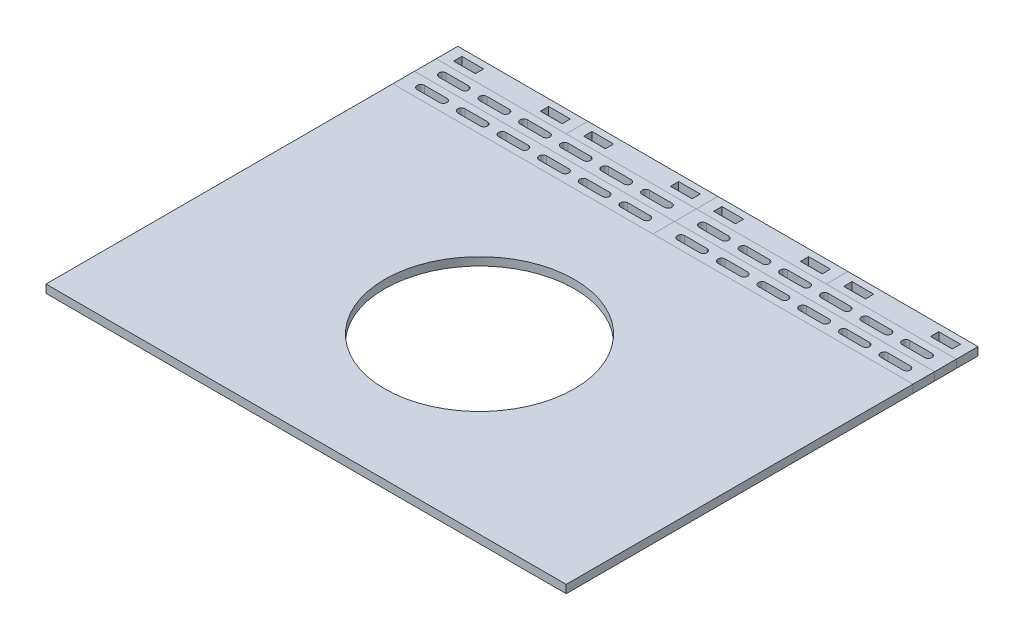
SolidWorks part; units mm, degrees
ref_plane "Front Plane" through (0, 0, 0) normal (0, 0, 1) x (1, 0, 0)
ref_plane "Top Plane" through (0, 0, 0) normal (0, 1, 0) x (1, 0, 0)
ref_plane "Right Plane" through (0, 0, 0) normal (1, 0, 0) x (0, 0, -1)
sketch "Sketch1" plane through (0, 0, 0) normal (0, 1, 0) x (1, 0, 0)
  line L0 (0, 0) -> (0, 203.2)
  line L1 (0, 0) -> (304.8, 0)
  line L5 (304.8, 203.2) -> (304.8, 0)
  line L6 (0, 203.2) -> (304.8, 203.2)
  line L7 (0, 101.6) -> (304.8, 101.6) construction
  line L8 (152.4, 203.2) -> (152.4, 0) construction
  circle A2 centre (152.4, 101.6) radius 55.5625
  point P11 (152.4, 101.6)
  dimension "D3" = 111.125
  dimension "D1" = 304.8
  dimension "D2" = 203.2
extrude "Boss-Extrude1" add sketch "Sketch1" along normal blind 4.7625
sketch "Sketch3" plane through (0, 0, 0) normal (0, 1, 0) x (1, 0, 0)
  line L0 (0, 203.2) -> (0, 215.9)
  line L1 (0, 215.9) -> (152.4, 215.9)
  line L2 (152.4, 215.9) -> (152.4, 203.2)
  line L3 (304.8, 203.2) -> (0, 203.2) construction
  line L4 (152.4, 203.2) -> (0, 203.2)
  dimension "D1" = 12.7
  dimension "D2" = 152.4
extrude "Boss-Extrude2" add sketch "Sketch3" along normal blind 4.7625 separate body
sketch "Sketch4" plane through (0, 4.7625, 0) normal (0, 1, 0) x (1, 0, 0)
  line L0 (10.0838, 209.55) -> (23.2537, 209.55) construction
  line L1 (10.0838, 211.6963) -> (23.2537, 211.6963)
  line L2 (10.0838, 207.4037) -> (23.2537, 207.4037)
  line L3 (10.0838, 215.9) -> (10.0838, 203.2) construction
  line L4 (152.4, 215.9) -> (0, 215.9) construction
  line L5 (304.8, 203.2) -> (0, 203.2) construction
  line L6 (7.9375, 209.55) -> (0, 209.55) construction
  line L7 (0, 215.9) -> (0, 203.2) construction
  arc A0 (10.0838, 211.6963) -> (10.0838, 207.4037) centre (10.0838, 209.55) ccw
  arc A1 (23.2537, 207.4037) -> (23.2537, 211.6963) centre (23.2537, 209.55) ccw
  point P2 (16.6687, 209.55)
  point P13 (25.4, 209.55)
  point P15 (10.0838, 209.55)
  dimension "D1" = 2.1463
  dimension "D2" = 7.9375
  dimension "D3" = 17.4625
extrude "Cut-Extrude1" cut sketch "Sketch4" against normal blind 4.7625
pattern_linear "LPattern2" count 6 spacing 23.8125 along (1, 0, 0) of "Cut-Extrude1"
pattern_linear "LPattern3" count 2 spacing 12.7 along (0, 0, -1) count 2 spacing 152.4 along (1, 0, 0) of bodies 104
sketch "Sketch5" plane through (0, 0, 0) normal (0, 1, 0) x (1, 0, 0)
  line L0 (0, 228.6) -> (0, 241.3)
  line L1 (0, 241.3) -> (76.2, 241.3)
  line L3 (76.2, 228.6) -> (0, 228.6)
  line L4 (152.4, 228.6) -> (0, 228.6) construction
  line L5 (76.2, 241.3) -> (76.2, 228.6)
  point P4 (76.2, 228.6)
  dimension "D1" = 12.7
extrude "Boss-Extrude3" add sketch "Sketch5" along normal blind 4.7625 separate body
sketch "Sketch6" plane through (0, 4.7625, 0) normal (0, 1, 0) x (1, 0, 0)
  line L0 (6.2992, 237.363) -> (6.2992, 232.537)
  line L1 (6.2992, 232.537) -> (19.05, 232.537)
  line L2 (19.05, 232.537) -> (19.05, 237.363)
  line L3 (19.05, 237.363) -> (6.2992, 237.363)
  line L4 (57.15, 237.363) -> (57.15, 232.537)
  line L5 (57.15, 232.537) -> (69.85, 232.537)
  line L6 (69.85, 232.537) -> (69.85, 237.363)
  line L7 (69.85, 237.363) -> (57.15, 237.363)
  line L8 (0, 234.95) -> (6.2992, 234.95) construction
  line L9 (0, 241.3) -> (0, 228.6) construction
  line L10 (19.05, 234.95) -> (57.15, 234.95) construction
  line L11 (38.1, 228.6) -> (38.1, 241.3) construction
  line L12 (152.4, 228.6) -> (0, 228.6) construction
  line L13 (76.2, 241.3) -> (0, 241.3) construction
  line L14 (0, 241.3) -> (76.2, 241.3) construction
  point P20 (38.1, 234.95)
  point P21 (38.1, 234.95)
  point P22 (38.1, 241.3)
  dimension "D1" = 38.1
  dimension "D2" = 12.7508
  dimension "D3" = 12.7
  dimension "D4" = 4.826
extrude "Cut-Extrude2" cut sketch "Sketch6" against normal blind 4.7625
pattern_linear "LPattern4" count 4 spacing 76.2 along (1, 0, 0) of bodies 109
